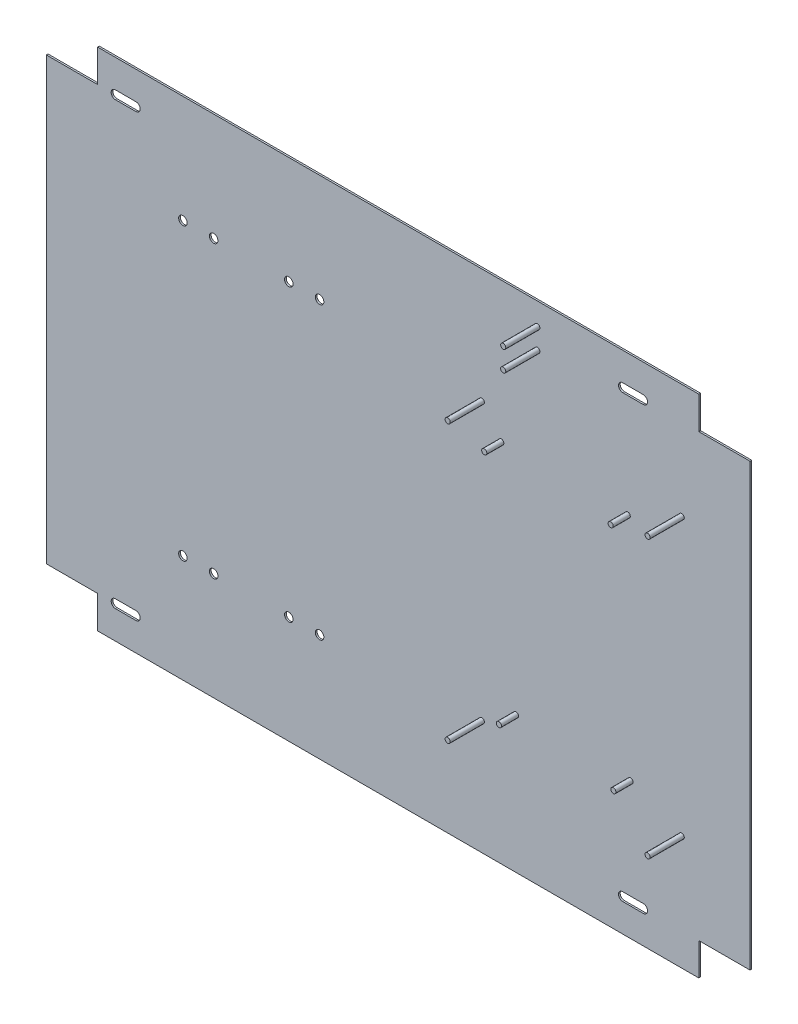
SolidWorks part; units mm, degrees
ref_plane "Alzado" through (0, 0, 0) normal (0, 0, 1) x (1, 0, 0)
ref_plane "Planta" through (0, 0, 0) normal (0, 1, 0) x (1, 0, 0)
ref_plane "Vista lateral" through (0, 0, 0) normal (1, 0, 0) x (0, 0, -1)
sketch "Croquis1" plane through (0, 0, 0) normal (0, 0, 1) x (1, 0, 0)
  line L0 (-206, 279) -> (-206, -7.4512) construction
  line L3 (-30, 279) -> (-382, 279)
  line L4 (-412, 2) -> (-412, 260)
  line L7 (-412, 260) -> (-382, 260)
  line L8 (-382, 279) -> (-382, 260)
  line L9 (0, 260) -> (-30, 260)
  line L10 (-30, 279) -> (-30, 260)
  line L11 (-412, 131) -> (85.2114, 131) construction
  line L12 (0, 2) -> (-30, 2)
  line L13 (-30, -17) -> (-30, 2)
  line L14 (-30, -17) -> (-382, -17)
  line L15 (-412, 2) -> (-382, 2)
  line L16 (-382, -17) -> (-382, 2)
  line L17 (0, 2) -> (0, 260)
  line L18 (-371.5, 260) -> (-359.5, 260) construction
  line L19 (-371.5, 262.5) -> (-359.5, 262.5)
  line L20 (-371.5, 257.5) -> (-359.5, 257.5)
  line L21 (-359.5, 260) -> (-349.65, 260) construction
  line L22 (-359.5, 260) -> (-383.4975, 260) construction
  line L23 (-371.5, 2) -> (-359.5, 2) construction
  line L24 (-371.5, -0.5) -> (-359.5, -0.5)
  line L25 (-371.5, 4.5) -> (-359.5, 4.5)
  arc A0 (-371.5, 262.5) -> (-371.5, 257.5) centre (-371.5, 260) ccw
  arc A1 (-359.5, 257.5) -> (-359.5, 262.5) centre (-359.5, 260) ccw
  arc A2 (-371.5, -0.5) -> (-371.5, 4.5) centre (-371.5, 2) cw
  arc A3 (-359.5, 4.5) -> (-359.5, -0.5) centre (-359.5, 2) cw
  point P19 (-365.5, 260)
  point P29 (-365.5, 2)
  dimension "D1" = 296
  dimension "D2" = 412
  dimension "D3" = 30
  dimension "D4" = 19
  dimension "D5" = 5
  dimension "D6" = 12
  dimension "D7" = 40.5
extrude "Saliente-Extruir1" add sketch "Croquis1" along normal blind 1
sketch "Croquis2" plane through (0, 0, 1) normal (0, 0, 1) x (1, 0, 0)
  line L0 (-62.5, 260) -> (-74.5, 260) construction
  line L1 (-62.5, 257.5) -> (-74.5, 257.5)
  line L2 (-62.5, 262.5) -> (-74.5, 262.5)
  line L3 (-30, 260) -> (-65.183, 260) construction
  line L4 (-30, 279) -> (-382, 279) construction
  line L5 (0, 131) -> (-412, 131) construction
  line L6 (0, 2) -> (0, 260) construction
  line L7 (-412, 260) -> (-412, 2) construction
  line L8 (-62.5, 2) -> (-74.5, 2) construction
  line L9 (-62.5, 4.5) -> (-74.5, 4.5)
  line L10 (-62.5, -0.5) -> (-74.5, -0.5)
  arc A0 (-62.5, 257.5) -> (-62.5, 262.5) centre (-62.5, 260) ccw
  arc A1 (-74.5, 262.5) -> (-74.5, 257.5) centre (-74.5, 260) ccw
  arc A2 (-62.5, 4.5) -> (-62.5, -0.5) centre (-62.5, 2) cw
  arc A3 (-74.5, -0.5) -> (-74.5, 4.5) centre (-74.5, 2) cw
  point P2 (-68.5, 260)
  point P12 (-60, 260)
  point P22 (-68.5, 2)
  dimension "D2" = 5
  dimension "D1" = 12
  dimension "D3" = 19
  dimension "D4" = 60
extrude "Cortar-Extruir1" cut sketch "Croquis2" against normal up to surface (1 mm away) contours L2 A1 L1 A0 | L9 A3 L10 A2 up to face at (-206, 131, 0)
sketch "Croquis3" plane through (0, 0, 1) normal (0, 0, 1) x (1, 0, 0)
  line L0 (-30, 279) -> (-382, 279) construction
  line L1 (0, 131) -> (-152.6566, 131) construction
  line L2 (0, 2) -> (0, 260) construction
  line L3 (-40, 212) -> (-40, 50) construction
  line L4 (-98.5, 174.8901) -> (-98.5, 104.997) construction
  line L5 (-157, 212) -> (-157, 50) construction
  circle A0 centre (-40, 212) radius 1.5
  circle A1 centre (-40, 50) radius 1.5
  circle A2 centre (-157, 50) radius 1.5
  circle A3 centre (-157, 212) radius 1.5
  dimension "D1" = 3
  dimension "D2" = 67
  dimension "D3" = 40
  dimension "D4" = 58.5
extrude "Saliente-Extruir5" add sketch "Croquis3" along normal blind 20 contours A3 | A0 | A2 | A1
sketch "Croquis4" plane through (0, 0, 1) normal (0, 0, 1) x (1, 0, 0)
  line L0 (0, 130) -> (-219.4361, 130) construction
  line L1 (-71.6, 197) -> (-71.6, 63) construction
  line L3 (0, 2) -> (0, 260) construction
  line L4 (-70, 63) -> (-147.5904, 63) construction
  line L5 (-71.6, 197) -> (-196.3993, 197) construction
  line L10 (-30, 279) -> (-382, 279) construction
  circle A0 centre (-71.6, 197) radius 1.5
  circle A3 centre (-70, 63) radius 1.5
  circle A4 centre (-137, 63) radius 1.5
  circle A5 centre (-145.6, 197) radius 1.5
  point P9 (-109.718, 130)
  dimension "D1" = 3
  dimension "D4" = 3
  dimension "D7" = 3
  dimension "D9" = 3
  dimension "D2" = 134
  dimension "D3" = 70
  dimension "D5" = 1.6
  dimension "D6" = 149
  dimension "D8" = 67
  dimension "D10" = 74
  dimension "D11" = 67
extrude "Saliente-Extruir6" add sketch "Croquis4" along normal blind 10 contours A0 | A5 | A4 | A3
sketch "Croquis5" plane through (0, 0, 1) normal (0, 0, 1) x (1, 0, 0)
  line L0 (-332, 216) -> (-332, 46) construction
  line L1 (-412, 131) -> (17.8188, 131) construction
  line L2 (-412, 260) -> (-412, 2) construction
  line L5 (-30, 279) -> (-382, 279) construction
  line L6 (-332, 216) -> (-314, 216) construction
  line L7 (-292, 131) -> (-292, 233.6242) construction
  circle A0 centre (-332, 216) radius 2.5
  circle A1 centre (-332, 46) radius 2.5
  circle A2 centre (-314, 216) radius 2.5
  circle A3 centre (-314, 46) radius 2.5
  circle A4 centre (-270, 46) radius 2.5
  circle A5 centre (-252, 46) radius 2.5
  circle A6 centre (-270, 216) radius 2.5
  circle A7 centre (-252, 216) radius 2.5
  point P4 (-332, 131)
  dimension "D1" = 5
  dimension "D2" = 5
  dimension "D6" = 5
  dimension "D3" = 170
  dimension "D4" = 18
  dimension "D5" = 148
  dimension "D7" = 40
  dimension "D8" = 80
extrude "Cortar-Extruir2" cut sketch "Croquis5" against normal up to surface (1 mm away) contours A0 | A2 | A7 | A6 | A5 | A4 | A3 | A1 up to face at (-68.5, 2, 0)
sketch "Croquis7" plane through (0, 0, 1) normal (0, 0, 1) x (1, 0, 0)
  line L0 (-124.5, 266) -> (-124.5, 254) construction
  line L3 (-30, 279) -> (-382, 279) construction
  circle A0 centre (-124.5, 266) radius 1.5
  circle A1 centre (-124.5, 254) radius 1.5
  arc A2 (-74.5, 262.5) -> (-74.5, 257.5) centre (-74.5, 260) ccw construction
  point P6 (-124.5, 260)
  dimension "D1" = 3
  dimension "D3" = 3
  dimension "D2" = 12
  dimension "D4" = 50
  dimension "D5" = 19
extrude "Saliente-Extruir7" add sketch "Croquis7" along normal blind 20 contours A0 | A1
